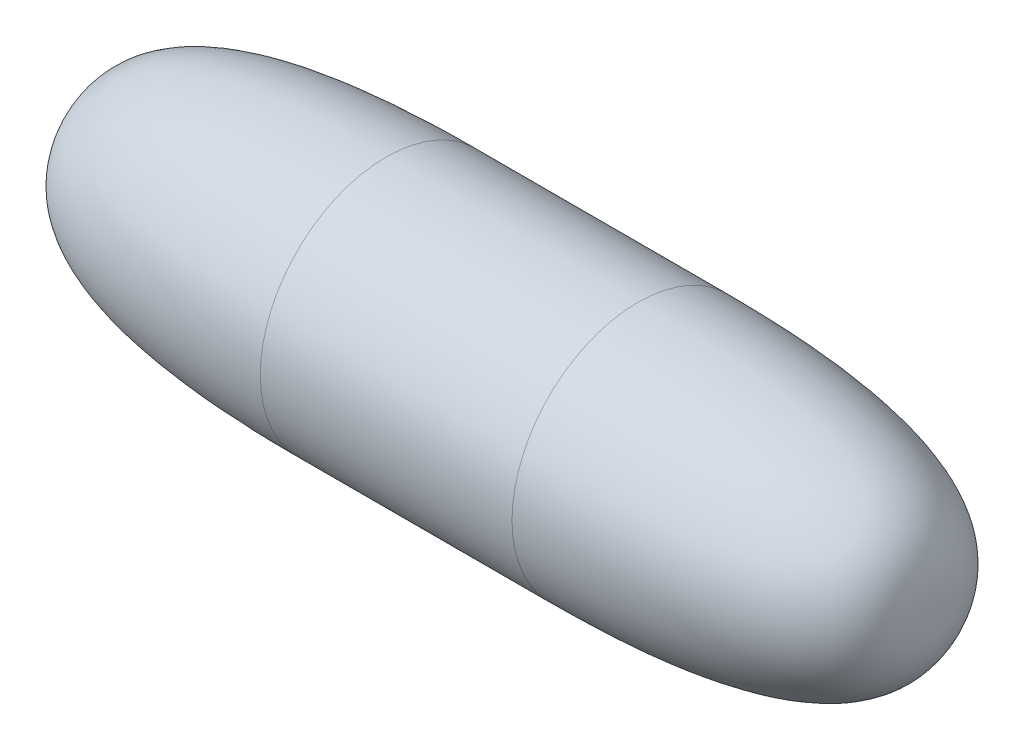
SolidWorks part; units mm, degrees
material "Plain Carbon Steel"
ref_plane "Front Plane" through (0, 0, 0) normal (0, 0, 1) x (1, 0, 0)
ref_plane "Top Plane" through (0, 0, 0) normal (0, 1, 0) x (1, 0, 0)
ref_plane "Right Plane" through (0, 0, 0) normal (1, 0, 0) x (0, 0, -1)
sketch "Sketch1" plane through (0, 0, 0) normal (0, 0, 1) x (1, 0, 0)
  line L0 (0, 0) -> (148.1422, 0) construction
  line L1 (0, 0) -> (0, 64.3269) construction
  line L2 (0, 0) -> (63.5, 0)
  line L3 (0, 19.05) -> (0, 0)
  line L4 (0, 19.05) -> (19.05, 19.05)
  line L5 (63.5, -36.6144) -> (63.5, 36.6144) construction
  line L6 (96.258, 19.05) -> (-0.4298, 19.05) construction
  spline S0 degree 3 poles (19.05, 19.05) (63.9088, 19.05) (63.5, 6.922) (63.5, 0) knots 0 0 0 0 1 1 1 1
  dimension "D1" = 38.1
  dimension "D2" = 127
  dimension "D3" = 19.05
revolve "Revolve1" add sketch "Sketch1" angle 360 about L0
mirror "Mirror1" about plane through (0, 19.05, 0) normal (1, 0, 0) of "Revolve1"
